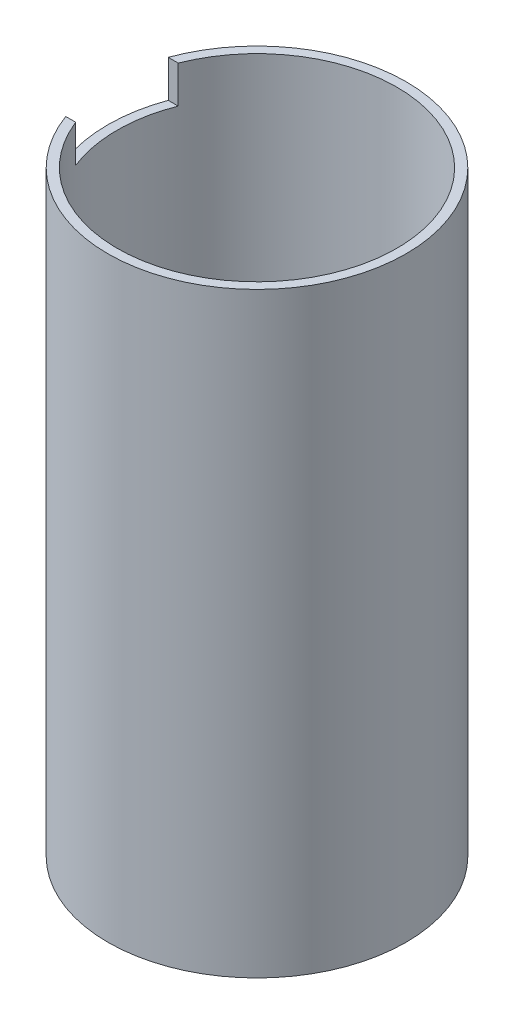
SolidWorks part; units mm, degrees
material "Aluminum Bronze"
ref_plane "Front Plane" through (0, 0, 0) normal (0, 0, 1) x (1, 0, 0)
ref_plane "Top Plane" through (0, 0, 0) normal (0, 1, 0) x (1, 0, 0)
ref_plane "Right Plane" through (0, 0, 0) normal (1, 0, 0) x (0, 0, -1)
sketch "Sketch1" plane through (0, 0, 0) normal (0, 1, 0) x (1, 0, 0)
  circle A0 centre (0, 0) radius 15
  circle A1 centre (0, 0) radius 16
  dimension "D1" = 30
  dimension "D2" = 32
extrude "Boss-Extrude1" add sketch "Sketch1" along normal blind 64
sketch "Sketch2" plane through (0, 64, 0) normal (0, 1, 0) x (1, 0, 0)
  line L0 (0, 0) -> (0, 5.5)
  line L1 (0, 0) -> (0, -5.5)
  line L2 (0, -5.5) -> (-16.8102, -5.5)
  line L3 (-16.8102, -5.5) -> (-16.8102, 5.5)
  line L4 (-16.8102, 5.5) -> (0, 5.5)
extrude "Cut-Extrude1" cut sketch "Sketch2" against normal blind 4
sketch "Sketch3" plane through (0, 0, 0) normal (0, -1, 0) x (1, 0, 0)
  line L0 (0, 0) -> (0, 5.5)
  line L1 (0, 0) -> (0, -5.5)
  line L2 (0, -5.5) -> (-17.0114, -5.5)
  line L3 (-17.0114, -5.5) -> (-17.0114, 5.5)
  line L4 (-17.0114, 5.5) -> (0, 5.5)
extrude "Cut-Extrude2" cut sketch "Sketch3" against normal blind 4
